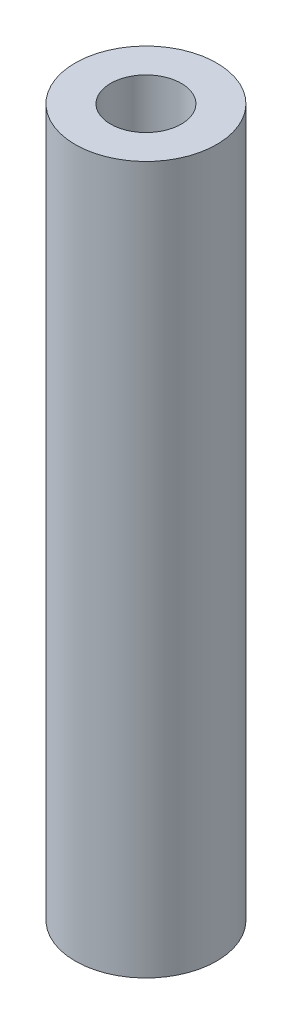
SolidWorks part; units mm, degrees
ref_plane "Front Plane" through (0, 0, 0) normal (0, 0, 1) x (1, 0, 0)
ref_plane "Top Plane" through (0, 0, 0) normal (0, 1, 0) x (1, 0, 0)
ref_plane "Right Plane" through (0, 0, 0) normal (1, 0, 0) x (0, 0, -1)
sketch "Sketch1" plane through (0, 0, 0) normal (0, 1, 0) x (1, 0, 0)
  circle A0 centre (0, 0) radius 3.175
  circle A1 centre (0, 0) radius 1.5875
  dimension "D1" = 6.35
  dimension "D2" = 3.175
extrude "Boss-Extrude1" add sketch "Sketch1" along normal blind 31.75
